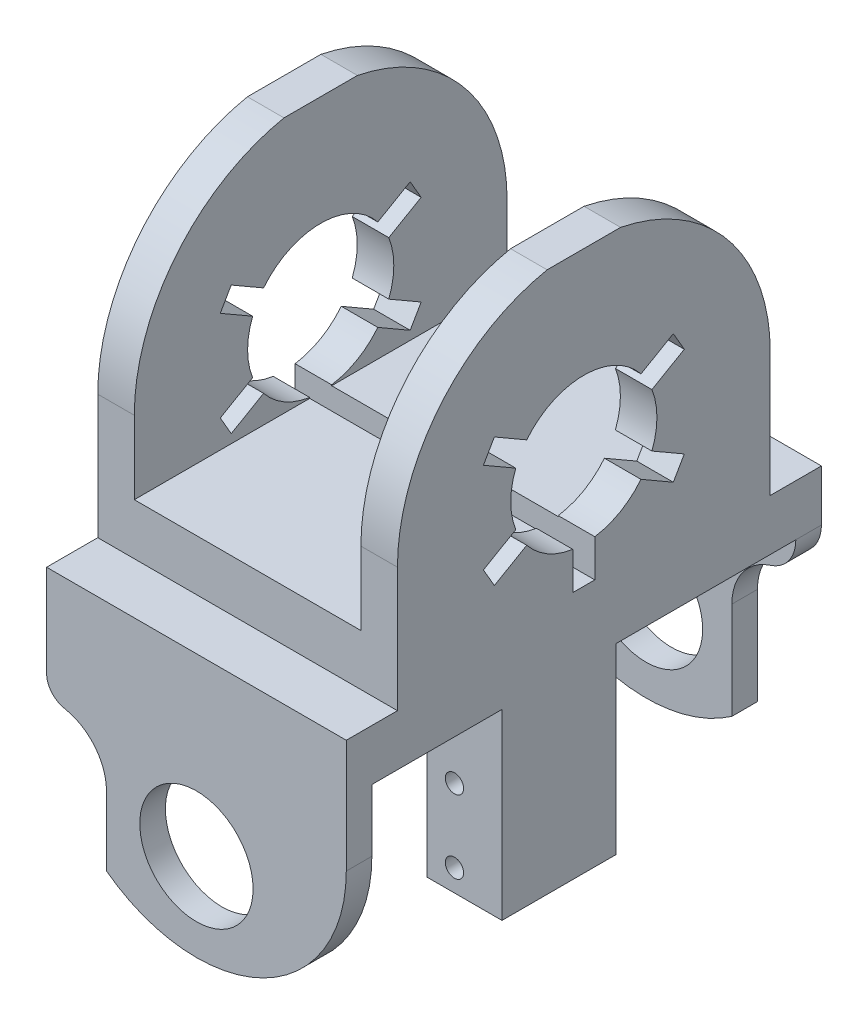
SolidWorks part; units mm, degrees
material "ABS"
ref_plane "Front Plane" through (0, 0, 0) normal (1, 0, 0) x (0, 1, 0)
ref_plane "Top Plane" through (0, 0, 0) normal (0, 0, 1) x (0, 1, 0)
ref_plane "Right Plane" through (0, 0, 0) normal (0, 1, 0) x (-1, 0, 0)
sketch "Sketch1" plane through (0, 0, 0) normal (1, 0, 0) x (0, 1, 0)
  line L0 (-38, 15.8457) -> (-38, -43721.3221) construction
  line L1 (-53, -32.5) -> (-17, -32.5)
  line L2 (-53, -32.5) -> (-53, -29)
  line L3 (-53, 32.5) -> (-17, 32.5)
  line L6 (-10, 0) -> (0, 0) construction
  line L7 (-53, 29) -> (-24, 29)
  line L9 (-53, -29) -> (-24, -29)
  line L10 (-24, 29) -> (-24, -29)
  line L11 (-3.6444, -9.3123) -> (-6.201, -13.7404)
  line L12 (-53, 29) -> (-53, 32.5)
  line L13 (-9.8869, -1.5) -> (-15, -1.5)
  line L14 (-17, 25.5) -> (0, 25.5)
  line L15 (-17, 32.5) -> (-17, 25.5)
  line L16 (-17, -25.5) -> (0, -25.5)
  line L18 (-17, -25.5) -> (-17, -32.5)
  line L20 (-9.8869, 1.5) -> (-15, 1.5)
  line L21 (-15, -1.5) -> (-15, 1.5)
  line L22 (-10, 1.5) -> (-10, -1.5) construction
  line L23 (-10, 0) -> (-15, 0) construction
  line L24 (0, 0) -> (-5.2488, 9.0911) construction
  line L25 (-8.2632, 6.7762) -> (-1.6413, 10.5994) construction
  line L26 (-6.2425, 7.8123) -> (-8.799, 12.2404)
  line L28 (-8.799, 12.2404) -> (-6.201, 13.7404)
  line L29 (-3.6444, 9.3123) -> (-6.201, 13.7404)
  line L30 (-6.2425, -7.8123) -> (-8.799, -12.2404)
  line L31 (-8.799, -12.2404) -> (-6.201, -13.7404)
  line L32 (0, -1000) -> (0, 49000) construction
  line L33 (6.2425, -7.8123) -> (8.799, -12.2404)
  line L34 (8.799, -12.2404) -> (6.201, -13.7404)
  line L35 (3.6444, -9.3123) -> (6.201, -13.7404)
  line L36 (8.799, 12.2404) -> (6.201, 13.7404)
  line L37 (6.2425, 7.8123) -> (8.799, 12.2404)
  line L38 (3.6444, 9.3123) -> (6.201, 13.7404)
  arc A0 (-9.8869, -1.5) -> (-6.2425, -7.8123) centre (0, 0) ccw
  arc A2 (-6.2425, 7.8123) -> (-9.8869, 1.5) centre (0, 0) ccw
  arc A3 (-3.6444, -9.3123) -> (3.6444, -9.3123) centre (0, 0) ccw
  arc A4 (3.6444, 9.3123) -> (-3.6444, 9.3123) centre (0, 0) ccw
  arc A5 (6.2425, -7.8123) -> (6.2425, 7.8123) centre (0, 0) ccw
  arc A6 (0, -25.5) -> (0, 25.5) centre (0, 0) ccw
  point P0 (0, 0)
  point P11 (-10, 0)
  dimension "D7" = 20
  dimension "D1" = 15
  dimension "D2" = 58
  dimension "D3" = 29
  dimension "D4" = 3.5
  dimension "D5" = 3.5
  dimension "D6" = 53
  dimension "D8" = 7
  dimension "D9" = 7
  dimension "D10" = 7
  dimension "D12" = 0
  dimension "D13" = 0
  dimension "D14" = 5
  dimension "D15" = 3
  dimension "D16" = 60
  dimension "D17" = 5
  dimension "D18" = 1.5
  dimension "D19" = 1.5
extrude "Boss-Extrude1" add sketch "Sketch1" along normal mid plane 41
sketch "Sketch2" plane through (0, 0, 0) normal (0, 0, 1) x (0, 1, 0)
  line L0 (0, 20.5) -> (-17, 20.5) construction
  line L1 (-10, 15.5) -> (25, 15.5)
  line L2 (-10, 15.5) -> (-10, -15.5)
  line L3 (-10, -15.5) -> (25, -15.5)
  line L5 (0, -20.5) -> (-17, -20.5) construction
  line L6 (-17, -20.5) -> (-17, 20.5) construction
  line L7 (-41, 20) -> (-41, -49980) construction
  line L8 (25, -15.5) -> (25, -20.5)
  line L9 (0, -20.5) -> (-17, -20.5) construction
  line L10 (-58, 25.5) -> (30, 25.5)
  line L11 (-53, -20.5) -> (-53, 20.5) construction
  line L12 (0, 0) -> (50000, 0) construction
  line L14 (-32.5, 20.5) -> (25, 20.5)
  line L16 (-32.5, -20.5) -> (25, -20.5)
  line L17 (25, 20.5) -> (25, 15.5)
  line L18 (-58, 25.5) -> (-58, -25.5)
  line L19 (-58, -25.5) -> (30, -25.5)
  line L20 (30, 25.5) -> (30, -25.5)
  circle A0 centre (-41, 0) radius 7.75
  arc A3 (-32.5, -20.5) -> (-32.5, 20.5) centre (-32.5, 0) cw
  point P30 (-53, 20.5)
other "AlignGroup1" parameters "D5"=1.4994, "D6"=10, "D1"=46.6161, "D2"=46.6161, "D3"=30, "D4"=30, "D7"=44.1265, "D8"=112, "D9"=112, "D10"=50, "D11"=112, "D12"=0, "D13"=73
extrude "Cut-Extrude1" cut sketch "Sketch2" against normal through all both and the other way through all contours A0 | L18 L10 L20 L19 | L8 L16 A3 L14 L17 L1 L2 L3
sketch "Sketch4" plane through (0, -24, 0) normal (0, -1, 0) x (1, 0, 0)
  line L0 (0, -1000) -> (0, 49000) construction
  line L1 (-1000, 0) -> (49000, 0) construction
  line L2 (20.5, -29) -> (-20.5, -29) construction
  line L3 (10.25, -4.4) -> (20.5, -4.4)
  line L4 (10.25, -4.4) -> (10.25, 11.2)
  line L5 (10.25, 11.2) -> (20.5, 11.2)
  line L6 (20.5, -4.4) -> (20.5, 11.2)
  line L7 (15.375, 11.2) -> (15.375, -4.4) construction
  line L8 (10.5, 0) -> (17.5, 0) construction
  line L9 (20.5, 29) -> (-20.5, 29) construction
  line L10 (-996.5066, -7.8) -> (49003.4934, -7.8) construction
  line L11 (20.5, 29) -> (20.5, -29) construction
  point P4 (15.375, 0)
  dimension "D1" = 10.25
  dimension "D2" = 24.6
  dimension "D4" = 17.8
  dimension "D5" = 3.4
extrude "Boss-Extrude2" add sketch "Sketch4" along normal blind 25
sketch "Sketch5" plane through (0, 0, -4.4) normal (0, 0, -1) x (1, 0, 0)
  line L0 (-1000, 41) -> (49000, 41) construction
  circle A0 centre (14, 46) radius 1.25
  circle A1 centre (14, 36) radius 1.25
  circle A2 centre (0, 41) radius 7.75 construction
  dimension "D2" = 2.5
  dimension "D1" = 5
  dimension "D3" = 14
extrude "Cut-Extrude2" cut sketch "Sketch5" against normal up to next
sketch "Sketch6" plane through (0, 0, -32.5) normal (0, 0, -1) x (1, 0, 0)
  line L0 (-1000, 41) -> (49000, 41) construction
  circle A0 centre (14, 46) radius 2.25
  circle A1 centre (14, 36) radius 2.25
  dimension "D1" = 4.5
extrude "Cut-Extrude3" cut sketch "Sketch6" against normal blind 29.3
sketch "Sketch7" plane through (0, 0, 32.5) normal (0, 0, 1) x (1, 0, 0)
  line L0 (-20.5, -17) -> (-20.5, -32.5) construction
  line L1 (-12.3049, -39.3972) -> (-12.3049, -48.8963)
  line L3 (-20.5, -29.6028) -> (-20.5, -41.8842)
  line L4 (-12.3049, -48.8963) -> (-20.5, -48.8963)
  line L5 (-20.5, -48.8963) -> (-20.5, -41.8842)
  arc A1 (-12.3049, -39.3972) -> (-18.0417, -32.5121) centre (-19.3049, -39.3972) ccw
  arc A2 (-20.5, -32.5) -> (20.5, -32.5) centre (0, -32.5) ccw construction
  arc A3 (-20.5, -29.6028) -> (-18.0417, -32.5121) centre (-17.5003, -29.5614) ccw
  dimension "D1" = 3
  dimension "D2" = 7
  dimension "D3" = 0.0414
extrude "Cut-Extrude4" cut sketch "Sketch7" against normal up to next
sketch "Sketch9" plane through (0, 0, -32.5) normal (0, 0, -1) x (1, 0, 0)
  line L4 (20.5, 32.5) -> (20.5, 17) construction
  line L5 (20.5, 49.2984) -> (20.5, 24)
  line L10 (11.75, 36) -> (11.75, 49.2984)
  line L11 (11.75, 49.2984) -> (20.5, 49.2984)
  arc A5 (11.75, 36) -> (17.0288, 28.7606) centre (19.3536, 36) ccw
  arc A6 (13.2677, 48.1275) -> (-20.5, 32.5) centre (0, 32.5) ccw construction
  circle A7 centre (14, 36) radius 2.25 construction
  arc A8 (17.0288, 28.7606) -> (20.5, 24) centre (15.5, 24) cw
  dimension "D1" = 5
extrude "Cut-Extrude5" cut sketch "Sketch9" against normal up to surface (3.5 mm away) up to face at (11.75, -36, -29)
